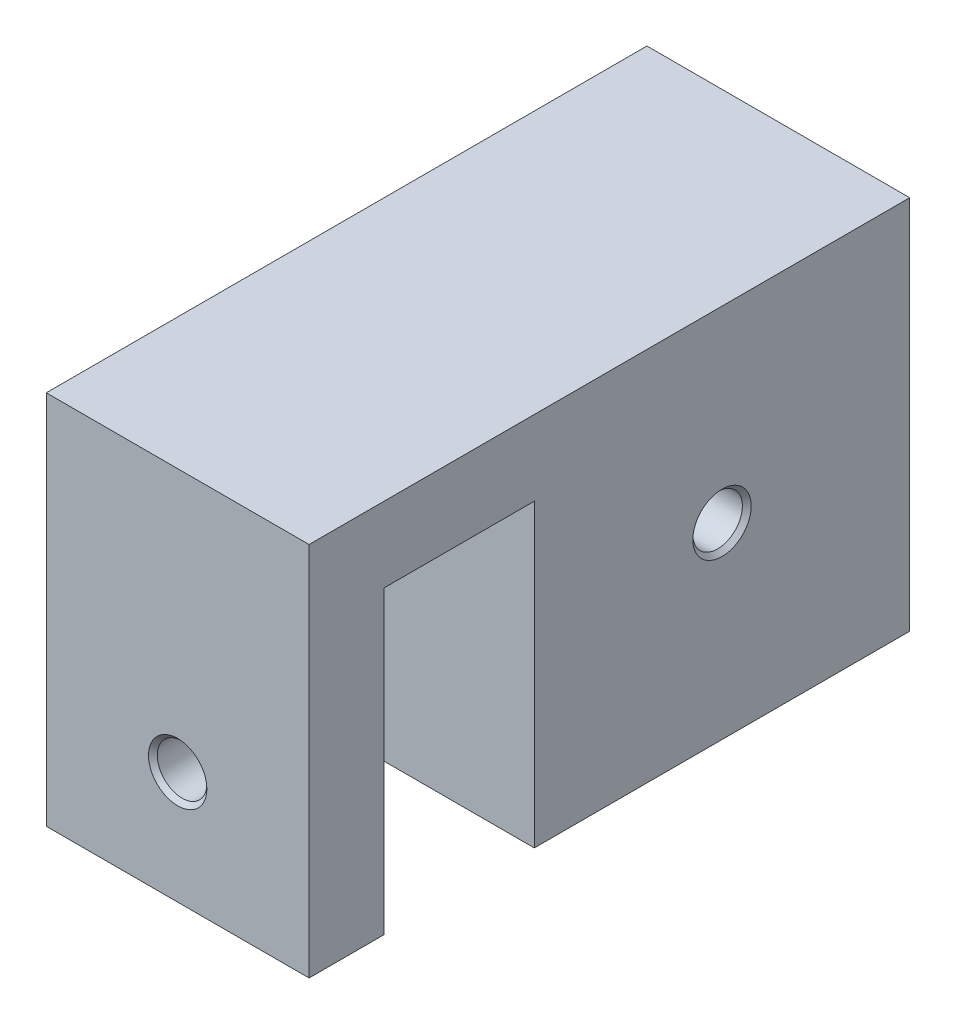
SolidWorks part; units mm, degrees
ref_plane "前视基准面" through (0, 0, 0) normal (0, 0, 1) x (1, 0, 0)
ref_plane "上视基准面" through (0, 0, 0) normal (0, 1, 0) x (1, 0, 0)
ref_plane "右视基准面" through (0, 0, 0) normal (1, 0, 0) x (0, 0, -1)
sketch "草图2" plane through (0, 0, 0) normal (1, 0, 0) x (0, 0, -1)
  line L1 (0, 0) -> (50, 0)
  line L2 (0, 0) -> (0, -50)
  line L3 (0, -50) -> (50, -50)
  line L4 (50, 0) -> (50, -50)
extrude "凸台-拉伸1" add sketch "草图2" along normal blind 35
sketch "草图3" plane through (0, 0, 0) normal (-1, 0, 0) x (0, 0, 1)
  circle A0 centre (-25, -25) radius 20
extrude "切除-拉伸1" cut sketch "草图3" against normal blind 20
hole_wizard "G1/16 螺纹孔1" positions "草图4" profile "草图5" tap size "G1/16" standard "GB"
sketch "草图4" plane through (35, 0, 0) normal (1, 0, 0) x (0, 0, -1)
  point P0 (25, -25)
sketch "草图5" plane through (35, -25, -25) normal (0, 1, 0) x (0, 0, -1)
  line L0 (0, 0) -> (0, 21.9828)
  line L1 (0, 21.9828) -> (3.3, 20)
  line L2 (3.3, 20) -> (3.3, 0.5865)
  line L3 (3.3, 0.5865) -> (3.8865, 0)
  line L5 (3.8865, 0) -> (0, 0)
  line L6 (-3.3, 0.5865) -> (-3.8865, 0) construction
  line L10 (0, 21.9828) -> (-3.3, 20) construction
  line L11 (0, -6.35) -> (0, 107.95) construction
  dimension "螺纹孔钻头直径" = 6.6
  dimension "螺纹孔钻头深度" = 20
  dimension "近端锥形沉头孔直径" = 7.773
  dimension "近端锥形沉头孔角度" = 90
  dimension "导头角度" = 118
cosmetic thread "孔螺蚊线1" parameters "D1"=15.45, "D2"=7.723
sketch "草图6" plane through (0, 0, -50) normal (0, 0, -1) x (-1, 0, 0)
  line L0 (0, -50) -> (0, 0) construction
  line L1 (-35, 0) -> (0, 0)
  line L2 (-35, 0) -> (-35, -10)
  line L3 (-35, -10) -> (0, -10)
  line L4 (0, 0) -> (0, -10)
sketch "草图14" plane through (0, 0, 0) normal (0, 0, 1) x (1, 0, 0)
  line L0 (0, 0) -> (0, -50) construction
  line L1 (35, 0) -> (0, 0)
  line L2 (35, 0) -> (35, -10)
  line L3 (35, -10) -> (0, -10)
  line L4 (0, 0) -> (0, -10)
extrude "凸台-拉伸4" add sketch "草图14" along normal blind 30
sketch "草图15" plane through (0, -10, 0) normal (0, -1, 0) x (-1, 0, 0)
  line L0 (-35, -30) -> (-35, 0) construction
  line L1 (0, -30) -> (-35, -30)
  line L2 (0, -30) -> (0, -20)
  line L3 (0, -20) -> (-35, -20)
  line L4 (-35, -30) -> (-35, -20)
extrude "凸台-拉伸5" add sketch "草图15" along normal blind 40
sketch "草图18" plane through (0, 0, 30) normal (0, 0, 1) x (1, 0, 0)
  line L0 (17.5, -50) -> (17.5, -35)
  line L1 (35, -50) -> (0, -50) construction
hole_wizard "G1/16 螺纹孔2" positions "草图19" profile "草图20" tap size "G1/16" standard "GB"
sketch "草图19" plane through (0, 0, 30) normal (0, 0, 1) x (1, 0, 0)
  point P0 (17.5, -35)
sketch "草图20" plane through (17.5, -35, 30) normal (1, 0, 0) x (0, -1, 0)
  line L0 (0, 0) -> (0, 21.9828)
  line L1 (0, 21.9828) -> (3.3, 20)
  line L2 (3.3, 20) -> (3.3, 0.5865)
  line L3 (3.3, 0.5865) -> (3.8865, 0)
  line L5 (3.8865, 0) -> (0, 0)
  line L6 (-3.3, 0.5865) -> (-3.8865, 0) construction
  line L10 (0, 21.9828) -> (-3.3, 20) construction
  line L11 (0, -6.35) -> (0, 107.95) construction
  dimension "螺纹孔钻头直径" = 6.6
  dimension "螺纹孔钻头深度" = 20
  dimension "近端锥形沉头孔直径" = 7.773
  dimension "近端锥形沉头孔角度" = 90
  dimension "导头角度" = 118
cosmetic thread "孔螺蚊线2" parameters "D1"=15.45, "D2"=7.723
